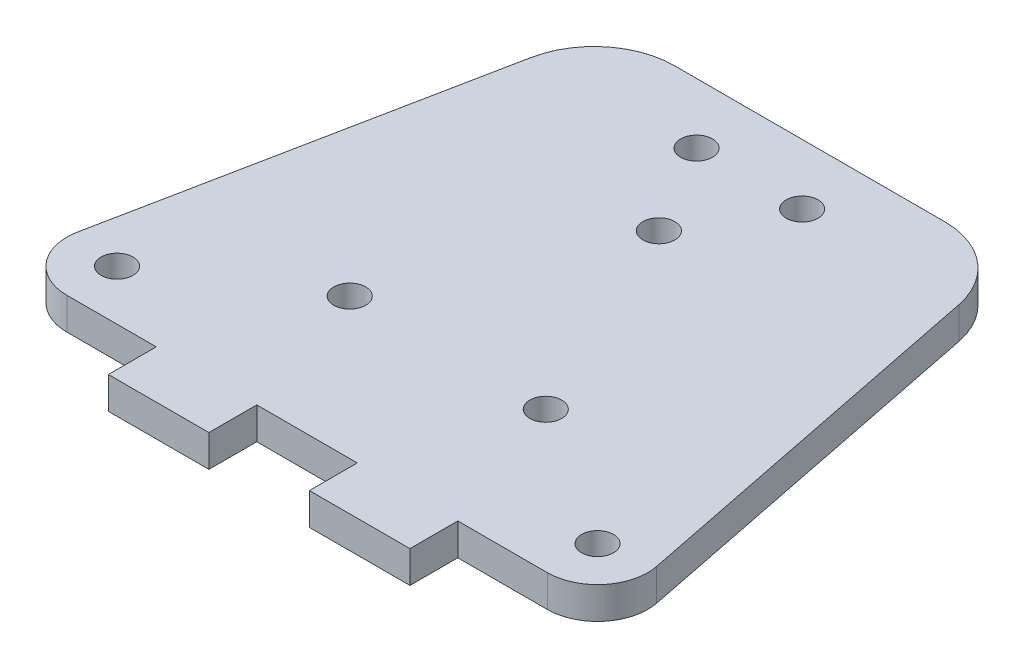
SolidWorks part; units mm, degrees
ref_plane "Alzado" through (0, 0, 0) normal (0, 0, 1) x (1, 0, 0)
ref_plane "Planta" through (0, 0, 0) normal (0, 1, 0) x (1, 0, 0)
ref_plane "Vista lateral" through (0, 0, 0) normal (1, 0, 0) x (0, 0, -1)
sketch "Croquis1" plane through (0, 0, 0) normal (0, 1, 0) x (1, 0, 0)
  line L0 (8.7138, 43.5689) -> (0, 0)
  line L1 (16.5584, 50) -> (43.4416, 50)
  line L3 (0, 0) -> (60, 0)
  line L5 (51.2862, 43.5689) -> (60, 0)
  line L11 (30, -1000) -> (30, 49000) construction
  circle A0 centre (20.25, 14) radius 9.5 construction
  circle A1 centre (39.75, 14) radius 9.5 construction
  circle A2 centre (20.25, 14) radius 12.5 construction
  circle A3 centre (39.75, 14) radius 12.5 construction
  circle A4 centre (39.75, 14) radius 1.5875
  circle A6 centre (20.25, 14) radius 1.5875
  circle A7 centre (24.75, 44) radius 1.5875
  circle A8 centre (35.25, 44) radius 1.5875
  circle A9 centre (24.75, 44) radius 4.7625 construction
  circle A10 centre (35.25, 44) radius 4.7625 construction
  arc A11 (51.2862, 43.5689) -> (43.4416, 50) centre (43.4416, 42) ccw
  arc A12 (8.7138, 43.5689) -> (16.5584, 50) centre (16.5584, 42) cw
  point P7 (50, 50)
  point P15 (30, 0)
  point P38 (10, 50)
  dimension "D6" = 19
  dimension "D7" = 19
  dimension "D5" = 25
  dimension "D10" = 25
  dimension "D20" = 3.175
  dimension "D21" = 3.175
  dimension "D22" = 3.175
  dimension "D26" = 9.525
  dimension "D27" = 9.525
  dimension "D29" = 8
  dimension "D12" = 3.175
  dimension "D1" = 60
  dimension "D3" = 40
  dimension "D4" = 20
  dimension "D8" = 19.5
  dimension "D9" = 14
  dimension "D11" = 9.75
  dimension "D23" = 4.5
  dimension "D24" = 4.5
  dimension "D25" = 30
  dimension "D28" = 50
extrude "Saliente-Extruir1" add sketch "Croquis1" along normal blind 3.175
sketch "Croquis2" plane through (0, 3.175, 0) normal (0, 1, 0) x (1, 0, 0)
  line L0 (0, 0) -> (60, 0) construction
  line L2 (60, 0) -> (51.2862, 43.5689) construction
  line L3 (53.901, 0) -> (60, 0)
  line L7 (43.4416, 50) -> (16.5584, 50)
  line L8 (8.7138, 43.5689) -> (0, 0)
  line L9 (0, 0) -> (60, 0)
  line L10 (60, 0) -> (51.2862, 43.5689)
  line L12 (1.1961, 5.9806) -> (0, 0)
  line L13 (0, 0) -> (6.099, 0)
  line L14 (60, 0) -> (58.8039, 5.9806)
  circle A0 centre (30, 35) radius 1.5875
  circle A1 centre (6.099, 5) radius 1.5875
  circle A2 centre (53.901, 5) radius 1.5875
  circle A3 centre (24.75, 44) radius 4.7625 construction
  circle A4 centre (35.25, 44) radius 4.7625 construction
  arc A6 (53.901, 0) -> (58.8039, 5.9806) centre (53.901, 5) ccw
  arc A7 (1.1961, 5.9806) -> (6.099, 0) centre (6.099, 5) ccw
  arc A9 (51.2862, 43.5689) -> (43.4416, 50) centre (43.4416, 42) ccw
  arc A10 (16.5584, 50) -> (8.7138, 43.5689) centre (16.5584, 42) ccw
  dimension "D1" = 9.525
  dimension "D2" = 9.525
  dimension "D3" = 3.175
  dimension "D4" = 3.175
  dimension "D5" = 3.175
  dimension "D6" = 5
  dimension "D7" = 10
  dimension "D9" = 5
  dimension "D10" = 30
  dimension "D11" = 35
  dimension "D8" = 0
extrude "Cortar-Extruir1" cut sketch "Croquis2" against normal blind 3.175
sketch "Croquis3" plane through (0, 3.175, 0) normal (0, 1, 0) x (1, 0, 0)
  line L0 (30, -1000) -> (30, 49000) construction
  line L1 (6.099, 0) -> (53.901, 0) construction
  line L3 (15, 0) -> (25, 0)
  line L4 (15, 0) -> (15, -4.7625)
  line L5 (15, -4.7625) -> (25, -4.7625)
  line L6 (25, 0) -> (25, -4.7625)
  line L7 (35, 0) -> (45, 0)
  line L8 (35, 0) -> (35, -4.7625)
  line L9 (35, -4.7625) -> (45, -4.7625)
  line L10 (45, 0) -> (45, -4.7625)
  point P5 (30, 0)
  dimension "D1" = 10
  dimension "D2" = 10
  dimension "D3" = 10
  dimension "D4" = 5
  dimension "D5" = 4.7625
extrude "Saliente-Extruir2" add sketch "Croquis3" against normal blind 3.175
